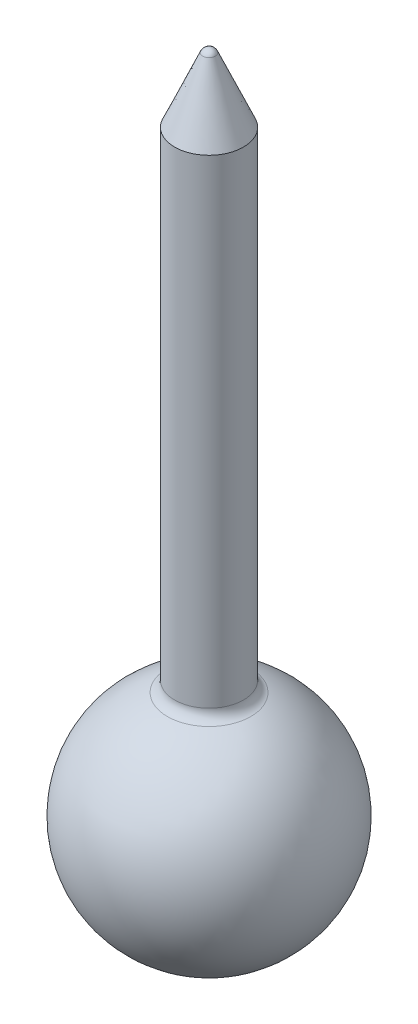
SolidWorks part; units mm, degrees
ref_plane "Спереди" through (0, 0, 0) normal (0, 0, 1) x (1, 0, 0)
ref_plane "Сверху" through (0, 0, 0) normal (0, 1, 0) x (1, 0, 0)
ref_plane "Справа" through (0, 0, 0) normal (1, 0, 0) x (0, 0, -1)
sketch "Эскиз1" plane through (0, 0, 0) normal (0, 0, 1) x (1, 0, 0)
  line L0 (0, 0) -> (0, 29.718) construction
  line L1 (1.5, 31) -> (0.2752, 33.8195)
  line L2 (1.5, 31) -> (1.5, 10.1235)
  line L3 (0, 34) -> (0, 32)
  line L4 (0.5, 31.5) -> (0.5, 10.1539)
  line L5 (0, 34) -> (-1.0369, 34) construction
  line L6 (0, 0) -> (0, 0.25)
  arc A0 (1.8182, 9.6577) -> (0, 0) centre (0, 5) cw
  arc A1 (0, 32) -> (0.5, 31.5) centre (0, 31.5) cw
  arc A2 (0, 0.25) -> (0.9048, 9.663) centre (0, 5) ccw
  arc A3 (0.2752, 33.8195) -> (0, 34) centre (0, 33.7) ccw
  arc A4 (1.8182, 9.6577) -> (1.5, 10.1235) centre (2, 10.1235) cw
  arc A5 (0.5, 10.1539) -> (0.9048, 9.663) centre (1, 10.1539) ccw
  dimension "D2" = 5
  dimension "D7" = 0.5
  dimension "D8" = 0.3
  dimension "D10" = 0.5
  dimension "D11" = 0.5
  dimension "D1" = 3
  dimension "D3" = 34
  dimension "D4" = 3
  dimension "D5" = 0.25
  dimension "D6" = 1
  dimension "D9" = 2
revolve "Повернуть1" add sketch "Эскиз1" angle 360 about L0
